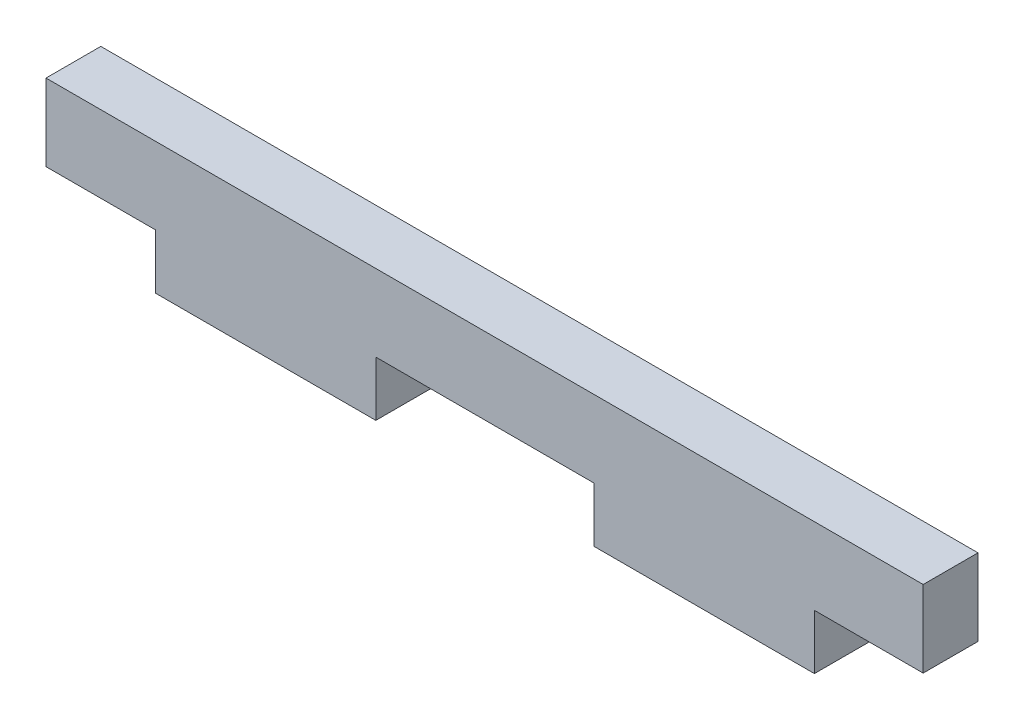
SolidWorks part; units mm, degrees
ref_plane "Front Plane" through (0, 0, 0) normal (0, 0, 1) x (1, 0, 0)
ref_plane "Top Plane" through (0, 0, 0) normal (0, 1, 0) x (1, 0, 0)
ref_plane "Right Plane" through (0, 0, 0) normal (1, 0, 0) x (0, 0, -1)
sketch "Sketch1" plane through (0, 0, 0) normal (0, 0, 1) x (1, 0, 0)
  line L0 (-6.2992, -2.2225) -> (6.35, -2.2225)
  line L1 (-25.4, 2.2225) -> (25.4, 2.2225)
  line L2 (-25.4, 2.2225) -> (-25.4, -2.2225)
  line L3 (-25.4, -2.2225) -> (-19.05, -2.2225)
  line L4 (25.4, 2.2225) -> (25.4, -2.2225)
  line L5 (-25.4, 2.2225) -> (25.4, -2.2225) construction
  line L6 (-25.4, -2.2225) -> (25.4, 2.2225) construction
  line L8 (-6.2992, -2.2225) -> (-6.2992, -5.3975)
  line L9 (-6.2992, -5.3975) -> (-19.05, -5.3975)
  line L10 (-19.05, -2.2225) -> (-19.05, -5.3975)
  line L12 (6.35, -2.2225) -> (6.35, -5.3975)
  line L13 (6.35, -5.3975) -> (19.1008, -5.3975)
  line L14 (19.1008, -2.2225) -> (19.1008, -5.3975)
  line L15 (19.1008, -2.2225) -> (25.4, -2.2225)
  point P0 (0, 0)
  point P14 (12.7254, -5.3975)
  point P15 (-12.6746, -5.3975)
  dimension "D1" = 4.445
  dimension "D2" = 50.8
  dimension "D3" = 3.175
  dimension "D4" = 12.7508
  dimension "D6" = 12.7508
  dimension "D7" = 6.35
  dimension "D5" = 25.4
extrude "Boss-Extrude1" add sketch "Sketch1" along normal mid plane 3.175
equation "\"D4@Sketch1\"=\"D6@Sketch1\""
equation "\"D5@Sketch1\"=\"D7@Sketch1\"*4"
equation "\"D2@Sketch1\"=\"D5@Sketch1\"*2"
